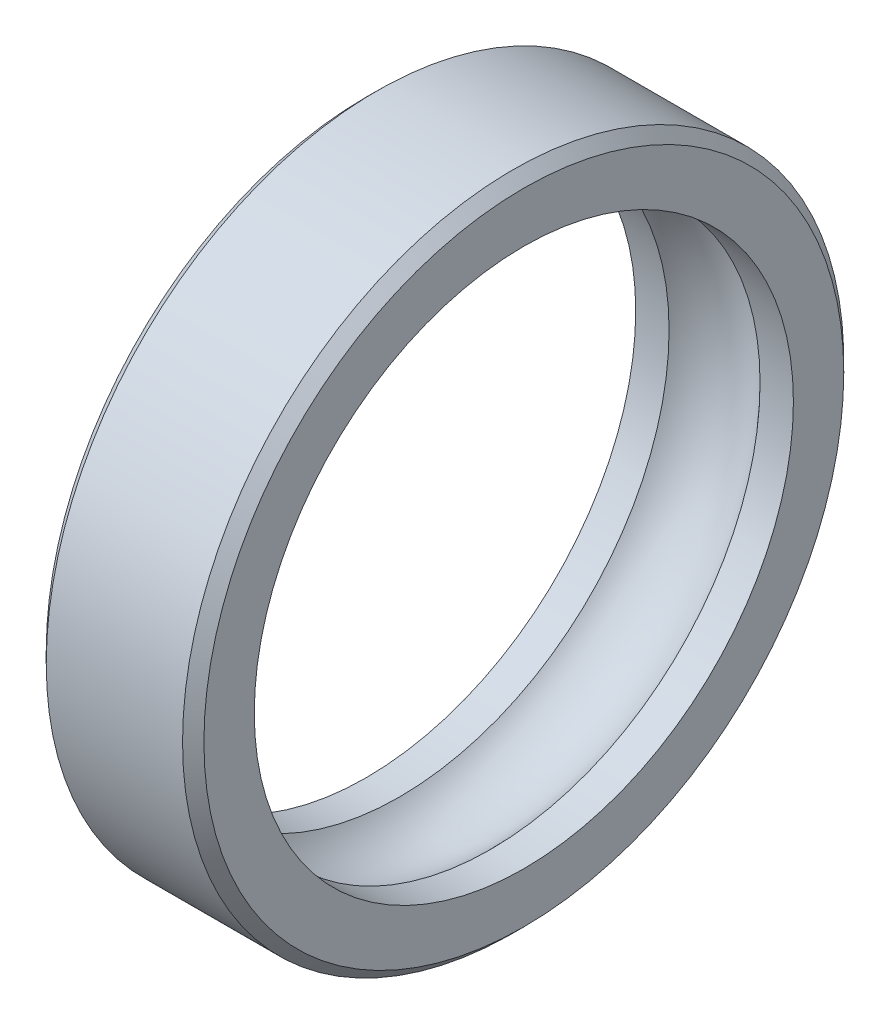
SolidWorks part; units mm, degrees
ref_plane "Front Plane" through (0, 0, 0) normal (0, 0, 1) x (1, 0, 0)
ref_plane "Top Plane" through (0, 0, 0) normal (0, 1, 0) x (1, 0, 0)
ref_plane "Right Plane" through (0, 0, 0) normal (1, 0, 0) x (0, 0, -1)
sketch "Sketch1" plane through (0, 0, 0) normal (0, 0, 1) x (1, 0, 0)
  line L0 (-47.3655, 0) -> (77.7343, 0) construction
  line L1 (0, 59) -> (0, 0) construction
  line L6 (-15.5, 65) -> (15.5, 65)
  line L7 (-15.5, 65) -> (-15.5, 53)
  line L9 (15.5, 65) -> (15.5, 53)
  line L10 (-15.5, 65) -> (15.5, 53) construction
  line L11 (-15.5, 53) -> (15.5, 65) construction
  line L12 (-8.9443, 53) -> (-15.5, 53)
  line L13 (8.9443, 53) -> (15.5, 53)
  arc A0 (-8.9443, 53) -> (8.9443, 53) centre (0, 45) cw
  point P3 (0, 59)
  dimension "D5" = 12
  dimension "D1" = 65
  dimension "D3" = 31
  dimension "D4" = 8
revolve "Revolve1" add sketch "Sketch1" angle 360 about L0
chamfer "Chamfer1" distance 2.1 angle 45 2 edges at (15.5, 0, 65) (-15.5, 0, 65)
